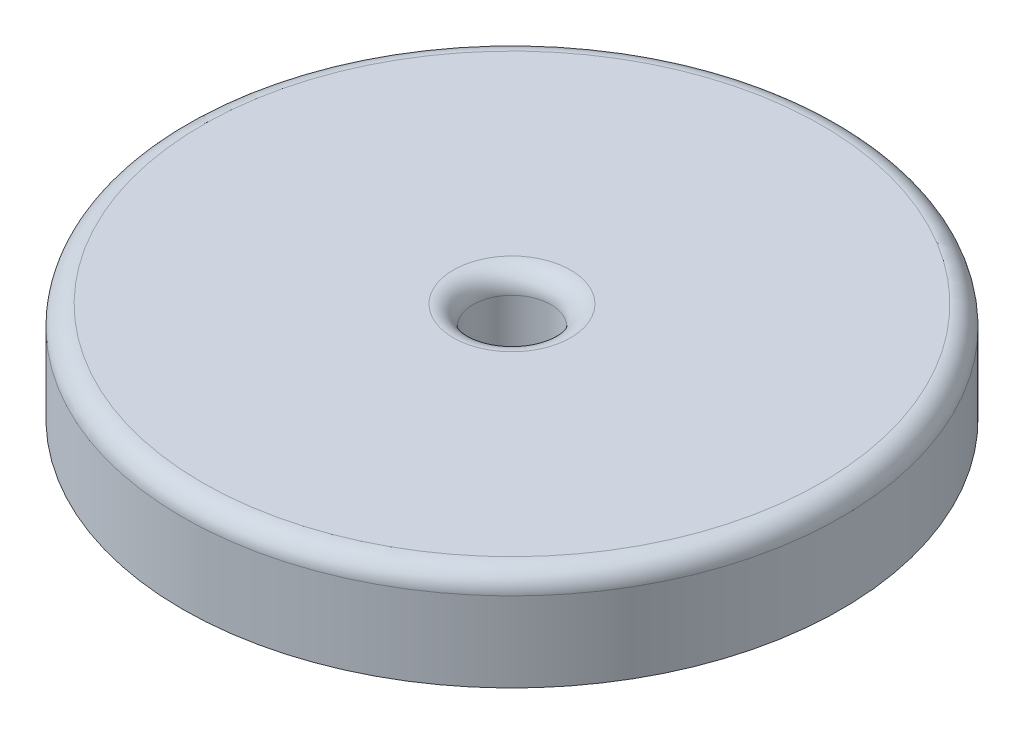
SolidWorks part; units mm, degrees
ref_plane "Front Plane" through (0, 0, 0) normal (0, 0, 1) x (1, 0, 0)
ref_plane "Top Plane" through (0, 0, 0) normal (0, 1, 0) x (1, 0, 0)
ref_plane "Right Plane" through (0, 0, 0) normal (1, 0, 0) x (0, 0, -1)
sketch "Sketch1" plane through (0, 0, 0) normal (0, 1, 0) x (1, 0, 0)
  circle A0 centre (0, 0) radius 33.0722
  dimension "D1" = 66.1443
extrude "Boss-Extrude1" add sketch "Sketch1" along normal blind 10
sketch "Sketch2" plane through (0, 10, 0) normal (0, 1, 0) x (1, 0, 0)
  circle A0 centre (0, 0) radius 3.89
  dimension "D1" = 7.78
extrude "Cut-Extrude1" cut sketch "Sketch2" against normal blind 8
sketch "Sketch3" plane through (0, 2, 0) normal (0, 1, 0) x (1, 0, 0)
  circle A0 centre (0, 0) radius 1.935
  dimension "D1" = 3.87
extrude "Cut-Extrude2" cut sketch "Sketch3" against normal blind 8
fillet "Fillet1" radius 2 1 edges at (0, 10, 33.0722)
fillet "Fillet2" radius 2 1 edges at (0, 10, 3.89)
